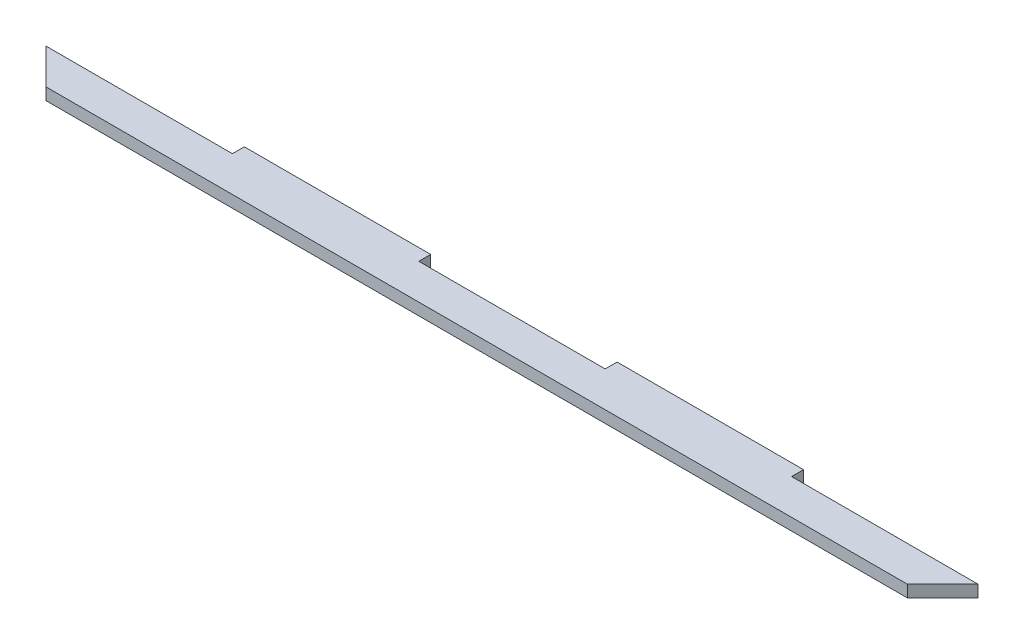
SolidWorks part; units mm, degrees
ref_plane "Front Plane" through (0, 0, 0) normal (0, 0, 1) x (1, 0, 0)
ref_plane "Top Plane" through (0, 0, 0) normal (0, 1, 0) x (1, 0, 0)
ref_plane "Right Plane" through (0, 0, 0) normal (1, 0, 0) x (0, 0, -1)
sketch "Sketch1" plane through (0, 0, 0) normal (0, 1, 0) x (1, 0, 0)
  line L0 (-37.0313, 2.7357) -> (5.1687, 2.7357)
  line L3 (-29.0313, -5.2643) -> (165.9687, -5.2643)
  line L5 (-37.0313, 2.7357) -> (-29.0313, -5.2643)
  line L6 (173.9687, 2.7357) -> (165.9687, -5.2643)
  line L7 (5.1687, 5.4357) -> (47.3687, 5.4357)
  line L8 (131.7687, 2.7357) -> (173.9687, 2.7357)
  line L9 (89.5687, 5.4357) -> (131.7687, 5.4357)
  line L11 (5.1687, 5.4357) -> (5.1687, 2.7357)
  line L12 (47.3687, 5.4357) -> (47.3687, 2.7357)
  line L13 (89.5687, 5.4357) -> (89.5687, 2.7357)
  line L14 (131.7687, 5.4357) -> (131.7687, 2.7357)
  line L15 (47.3687, 2.7357) -> (89.5687, 2.7357)
  point P0 (0, 0)
extrude "Boss-Extrude1" add sketch "Sketch1" along normal blind 2.7
